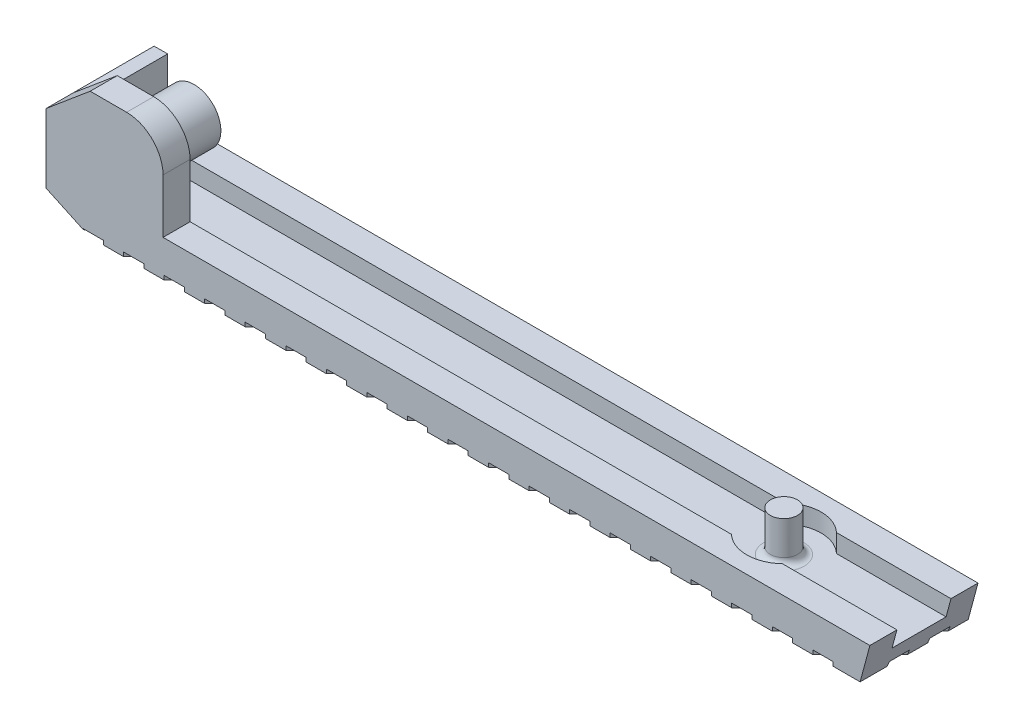
SolidWorks part; units mm, degrees
ref_plane "Front Plane" through (0, 0, 0) normal (0, 0, 1) x (1, 0, 0)
ref_plane "Top Plane" through (0, 0, 0) normal (0, 1, 0) x (1, 0, 0)
ref_plane "Right Plane" through (0, 0, 0) normal (1, 0, 0) x (0, 0, -1)
sketch "Sketch1" plane through (0, 0, 0) normal (0, 0, 1) x (1, 0, 0)
  circle A0 centre (0, 0) radius 1.975
  dimension "D1" = 3.95
extrude "Boss-Extrude1" add sketch "Sketch1" along normal blind 3
sketch "Sketch2" plane through (0, 0, 3) normal (0, 0, 1) x (1, 0, 0)
  circle A0 centre (0, 0) radius 1
  dimension "D1" = 2
extrude "Cut-Extrude1" cut sketch "Sketch2" against normal through all
sketch "Sketch3" plane through (0, 0, 3) normal (0, 0, 1) x (1, 0, 0)
  line L0 (0, 0) -> (0, -4) construction
  line L1 (2.6963, 0.0273) -> (2.6965, -3.9727)
  line L3 (-2.6965, -6.6691) -> (-5.9659, -5.1446)
  line L4 (2.6965, -3.9727) -> (55, -3.9727)
  line L6 (0, -6.6691) -> (54.2775, -6.6691)
  line L8 (0, 2.6965) -> (-2.6965, 2.6965)
  line L10 (0, -6.6691) -> (-2.6965, -6.6691)
  line L12 (-5.9659, -5.1446) -> (-5.9659, -0.0469)
  line L13 (-5.9659, -0.0469) -> (-2.6965, 2.6965)
  line L14 (-2.6965, -6.6691) -> (-2.6965, 2.6965) construction
  line L15 (55, -3.9727) -> (54.2775, -6.6691)
  arc A0 (2.6963, 0.0273) -> (0, 2.6965) centre (0, 0) ccw
  point P3 (0, -2)
  dimension "D6" = 2.6965
  dimension "D1" = 4
  dimension "D3" = 65
  dimension "D4" = 2.6965
  dimension "D5" = 4
  dimension "D7" = 2.6965
  dimension "D8" = 2.6965
  dimension "D9" = 50
extrude "Boss-Extrude3" add sketch "Sketch3" along normal blind 2
sketch "Sketch4" plane through (0, 0, 3) normal (0, 0, -1) x (-1, 0, 0)
  line L1 (5.9659, -0.0469) -> (4.9659, -0.0469)
  line L2 (5.9659, -0.0469) -> (5.9659, -5.1446)
  line L3 (5.9659, -5.1446) -> (4.9659, -5.1446)
  line L4 (4.9659, -0.0469) -> (4.9659, -5.1446)
  dimension "D1" = 1
extrude "Boss-Extrude5" add sketch "Sketch4" along normal blind 6
sketch "Sketch5" plane through (0, 0, 3) normal (0, 0, -1) x (-1, 0, 0)
  line L0 (-54.6387, -5.3209) -> (2.6901, -5.3209)
  line L1 (-54.2775, -6.6691) -> (-55, -3.9727) construction
  line L2 (2.6901, -5.3209) -> (4.9659, -4.2597)
  line L3 (4.9659, -0.0469) -> (4.9659, -5.1446) construction
  line L4 (5.9659, -5.1446) -> (2.6965, -6.6691) construction
  line L5 (2.6965, -6.6691) -> (-54.2775, -6.6691) construction
  line L6 (4.9659, -4.2597) -> (4.9659, -5.1446)
  line L7 (4.9659, -5.1446) -> (5.9659, -5.1446)
  line L8 (5.9659, -5.1446) -> (2.6965, -6.6691)
  line L9 (2.6965, -6.6691) -> (-54.2775, -6.6691)
  line L10 (-54.2775, -6.6691) -> (-54.6387, -5.3209)
extrude "Boss-Extrude6" add sketch "Sketch5" along normal blind 6
sketch "Sketch6" plane through (0, 0, -3) normal (0, 0, -1) x (-1, 0, 0)
  line L0 (-54.6387, -5.3209) -> (-55, -3.9727)
  line L1 (-55, -3.9727) -> (2.6203, -3.9727)
  line L2 (2.6203, -3.9727) -> (4.9659, -2.8789)
  line L3 (4.9659, -0.0469) -> (4.9659, -4.2597) construction
  line L4 (4.9659, -4.2597) -> (2.6901, -5.3209) construction
  line L5 (-54.6387, -5.3209) -> (2.6901, -5.3209)
  line L6 (2.6901, -5.3209) -> (4.9659, -4.2597)
  line L7 (4.9659, -4.2597) -> (4.9659, -2.8789)
extrude "Boss-Extrude7" add sketch "Sketch6" against normal blind 2
sketch "Sketch7" plane through (0, -5.3209, 0) normal (0, 1, 0) x (1, 0, 0)
  line L0 (54.6387, -1) -> (44.6387, -1) construction
  line L1 (54.6387, 1) -> (54.6387, -3) construction
  dimension "D1" = 10
sketch "Sketch8" plane through (0, -5.3209, 0) normal (0, 1, 0) x (1, 0, 0)
  circle A0 centre (44.6387, -1) radius 1
  dimension "D1" = 2
extrude "Boss-Extrude8" add sketch "Sketch8" along normal blind 3
sketch "Sketch9" plane through (0, -5.3209, 0) normal (0, 1, 0) x (1, 0, 0)
  circle A0 centre (44.6387, -1) radius 2.75
  circle A1 centre (44.6387, -1) radius 1
  dimension "D1" = 5.5
extrude "Cut-Extrude2" cut sketch "Sketch9" along normal blind 3
fillet "Fillet1" radius 0.5 1 edges at (44.6387, -5.3209, 0)
sketch "Sketch10" plane through (0, -6.6691, 0) normal (0, -1, 0) x (1, 0, 0)
  line L0 (54.2775, -3) -> (46.2775, 5)
  line L1 (-2.6965, 5) -> (54.2775, 5) construction
  line L2 (46.2775, 5) -> (44.7775, 5)
  line L3 (44.7775, 5) -> (52.7775, -3)
  line L4 (54.2775, -3) -> (-2.6965, -3) construction
  line L5 (52.7775, -3) -> (54.2775, -3)
  line L6 (54.2775, 5) -> (54.2775, -3) construction
  line L7 (49.7775, -3) -> (51.2775, -3)
  line L8 (51.2775, -3) -> (43.2775, 5)
  line L9 (43.2775, 5) -> (41.7775, 5)
  line L10 (41.7775, 5) -> (49.7775, -3)
  line L11 (46.7775, -3) -> (48.2775, -3)
  line L12 (48.2775, -3) -> (40.2775, 5)
  line L13 (40.2775, 5) -> (38.7775, 5)
  line L14 (38.7775, 5) -> (46.7775, -3)
  line L15 (43.7775, -3) -> (45.2775, -3)
  line L16 (45.2775, -3) -> (37.2775, 5)
  line L17 (37.2775, 5) -> (35.7775, 5)
  line L18 (35.7775, 5) -> (43.7775, -3)
  line L19 (40.7775, -3) -> (42.2775, -3)
  line L20 (42.2775, -3) -> (34.2775, 5)
  line L21 (34.2775, 5) -> (32.7775, 5)
  line L22 (32.7775, 5) -> (40.7775, -3)
  line L23 (37.7775, -3) -> (39.2775, -3)
  line L24 (39.2775, -3) -> (31.2775, 5)
  line L25 (31.2775, 5) -> (29.7775, 5)
  line L26 (29.7775, 5) -> (37.7775, -3)
  line L27 (34.7775, -3) -> (36.2775, -3)
  line L28 (36.2775, -3) -> (28.2775, 5)
  line L29 (28.2775, 5) -> (26.7775, 5)
  line L30 (26.7775, 5) -> (34.7775, -3)
  line L31 (31.7775, -3) -> (33.2775, -3)
  line L32 (33.2775, -3) -> (25.2775, 5)
  line L33 (25.2775, 5) -> (23.7775, 5)
  line L34 (23.7775, 5) -> (31.7775, -3)
  line L35 (28.7775, -3) -> (30.2775, -3)
  line L36 (30.2775, -3) -> (22.2775, 5)
  line L37 (22.2775, 5) -> (20.7775, 5)
  line L38 (20.7775, 5) -> (28.7775, -3)
  line L39 (25.7775, -3) -> (27.2775, -3)
  line L40 (27.2775, -3) -> (19.2775, 5)
  line L41 (19.2775, 5) -> (17.7775, 5)
  line L42 (17.7775, 5) -> (25.7775, -3)
  line L43 (22.7775, -3) -> (24.2775, -3)
  line L44 (24.2775, -3) -> (16.2775, 5)
  line L45 (16.2775, 5) -> (14.7775, 5)
  line L46 (14.7775, 5) -> (22.7775, -3)
  line L47 (19.7775, -3) -> (21.2775, -3)
  line L48 (21.2775, -3) -> (13.2775, 5)
  line L49 (13.2775, 5) -> (11.7775, 5)
  line L50 (11.7775, 5) -> (19.7775, -3)
  line L51 (16.7775, -3) -> (18.2775, -3)
  line L52 (18.2775, -3) -> (10.2775, 5)
  line L53 (10.2775, 5) -> (8.7775, 5)
  line L54 (8.7775, 5) -> (16.7775, -3)
  line L55 (13.7775, -3) -> (15.2775, -3)
  line L56 (15.2775, -3) -> (7.2775, 5)
  line L57 (7.2775, 5) -> (5.7775, 5)
  line L58 (5.7775, 5) -> (13.7775, -3)
  line L59 (10.7775, -3) -> (12.2775, -3)
  line L60 (12.2775, -3) -> (4.2775, 5)
  line L61 (4.2775, 5) -> (2.7775, 5)
  line L62 (2.7775, 5) -> (10.7775, -3)
  line L63 (7.7775, -3) -> (9.2775, -3)
  line L64 (9.2775, -3) -> (1.2775, 5)
  line L65 (1.2775, 5) -> (-0.2225, 5)
  line L66 (-0.2225, 5) -> (7.7775, -3)
  line L67 (4.7775, -3) -> (6.2775, -3)
  line L68 (6.2775, -3) -> (-1.7225, 5)
  line L69 (-1.7225, 5) -> (-3.2225, 5)
  line L70 (-3.2225, 5) -> (4.7775, -3)
  line L71 (1.7775, -3) -> (3.2775, -3)
  line L72 (3.2775, -3) -> (-4.7225, 5)
  line L73 (-4.7225, 5) -> (-6.2225, 5)
  line L74 (-6.2225, 5) -> (1.7775, -3)
  line L75 (-1.2225, -3) -> (0.2775, -3)
  line L76 (0.2775, -3) -> (-7.7225, 5)
  line L77 (-7.7225, 5) -> (-9.2225, 5)
  line L78 (-9.2225, 5) -> (-1.2225, -3)
  line L79 (55.7775, -3) -> (57.2775, -3)
  line L80 (57.2775, -3) -> (49.2775, 5)
  line L81 (49.2775, 5) -> (47.7775, 5)
  line L82 (47.7775, 5) -> (55.7775, -3)
  line L83 (58.7775, -3) -> (60.2775, -3)
  line L84 (60.2775, -3) -> (52.2775, 5)
  line L85 (52.2775, 5) -> (50.7775, 5)
  line L86 (50.7775, 5) -> (58.7775, -3)
  dimension "D1" = 45
  dimension "D2" = 1.5
  dimension "D3" = 19
  dimension "D4" = 3
extrude "Cut-Extrude5" cut sketch "Sketch10" against normal blind 0.3
